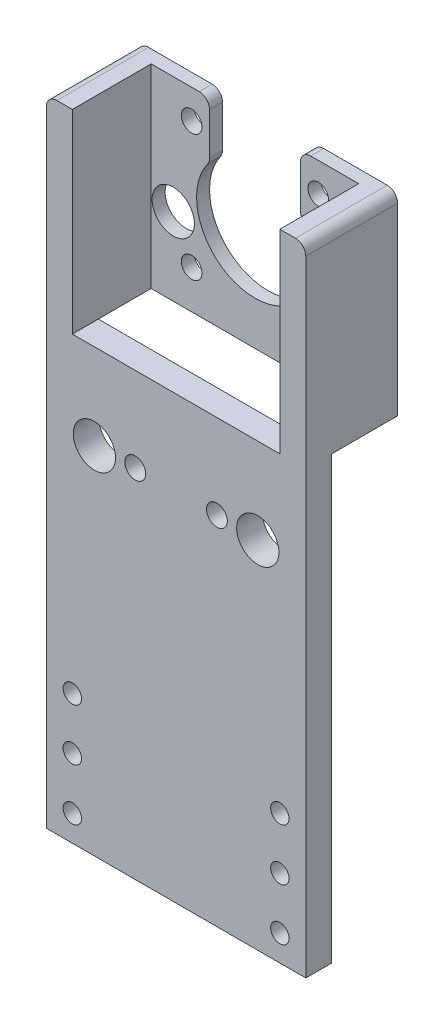
SolidWorks part; units mm, degrees
other "Markup1"
sketch "Sketch16" plane through (-31.75, 101.6, 0) normal (-0.1781, 0.3829, 0.9065) x (0.9824, 0.1222, 0.1414)
material "PLA White"
ref_plane "Front Plane" through (0, 0, 0) normal (0, 0, 1) x (1, 0, 0)
ref_plane "Top Plane" through (0, 0, 0) normal (0, 1, 0) x (1, 0, 0)
ref_plane "Right Plane" through (0, 0, 0) normal (1, 0, 0) x (0, 0, -1)
sketch "Sketch1" plane through (0, 0, 0) normal (1, 0, 0) x (0, 0, -1)
  line L2 (0, -53.975) -> (0, 53.975)
  line L4 (6.35, -53.975) -> (6.35, 53.975)
  line L15 (6.35, -53.975) -> (0, -53.975)
  line L24 (6.35, 53.975) -> (0, 53.975)
  point P14 (0, 0)
  dimension "D3" = 6.35
  dimension "D4" = 107.95
extrude "Boss-Extrude1" add sketch "Sketch1" along normal mid plane 63.5
sketch "Sketch2" plane through (0, 0, 0) normal (0, 0, 1) x (1, 0, 0)
  line L0 (-25.4, 95.25) -> (-25.4, 101.6) construction
  line L2 (-31.75, 53.975) -> (-31.75, 101.6)
  line L3 (-31.75, 101.6) -> (-25.4, 101.6)
  line L4 (-25.4, 53.975) -> (-25.4, 95.25)
  line L5 (-25.4, 101.6) -> (25.4, 101.6)
  line L7 (-25.4, 95.25) -> (25.4, 95.25)
  line L10 (31.75, 53.975) -> (31.75, 101.6)
  line L11 (31.75, 101.6) -> (25.4, 101.6)
  line L12 (25.4, 53.975) -> (25.4, 95.25)
  line L13 (31.75, 53.975) -> (-31.75, 53.975) construction
  line L18 (-31.75, 53.975) -> (-25.4, 53.975)
  line L19 (25.4, 53.975) -> (31.75, 53.975)
  dimension "D1" = 6.35
  dimension "D2" = 41.275
extrude "Boss-Extrude2" add sketch "Sketch2" against normal blind 19.304
sketch "Sketch3" plane through (0, 0, -19.304) normal (0, 0, -1) x (-1, 0, 0)
  line L1 (-31.75, 101.6) -> (31.75, 101.6)
  line L2 (-31.75, 101.6) -> (-31.75, 53.975)
  line L3 (-31.75, 53.975) -> (31.75, 53.975)
  line L4 (31.75, 101.6) -> (31.75, 53.975)
extrude "Boss-Extrude3" add sketch "Sketch3" along normal blind 3.175
sketch "Sketch5" plane through (0, 0, -22.479) normal (0, 0, -1) x (-1, 0, 0)
  line L0 (-11.1125, 87.9053) -> (-11.1125, 101.6)
  line L1 (31.75, 101.6) -> (-31.75, 101.6) construction
  line L2 (-11.1125, 101.6) -> (11.1125, 101.6)
  line L3 (11.1125, 101.6) -> (11.1125, 87.9053)
  arc A0 (11, 78.925) -> (-11, 78.925) centre (0, 78.925) ccw construction
  arc A1 (16.75, 63.425) -> (14.25, 63.425) centre (15.5, 63.425) ccw construction
  arc A2 (-14.25, 63.425) -> (-16.75, 63.425) centre (-15.5, 63.425) ccw construction
  arc A3 (-16.75, 94.425) -> (-14.25, 94.425) centre (-15.5, 94.425) ccw construction
  arc A4 (16.75, 94.425) -> (14.25, 94.425) centre (15.5, 94.425) ccw construction
  arc A5 (11, 78.925) -> (-11, 78.925) centre (0, 78.925) ccw construction
  arc A6 (16.75, 63.425) -> (14.25, 63.425) centre (15.5, 63.425) ccw construction
  arc A7 (-14.25, 63.425) -> (-16.75, 63.425) centre (-15.5, 63.425) ccw construction
  arc A8 (-16.75, 94.425) -> (-14.25, 94.425) centre (-15.5, 94.425) ccw construction
  arc A9 (16.75, 94.425) -> (14.25, 94.425) centre (15.5, 94.425) ccw construction
  arc A10 (-11.1125, 87.9053) -> (11.1125, 87.9053) centre (0, 78.925) ccw
  circle A11 centre (15.5, 94.425) radius 2.54
  circle A12 centre (15.5, 63.425) radius 2.54
  circle A13 centre (-15.5, 63.425) radius 2.54
  circle A14 centre (-15.5, 94.425) radius 2.54
  dimension "D1" = 5.08
  dimension "D2" = 28.575
  dimension "D3" = 22.225
extrude "Cut-Extrude2" cut sketch "Sketch5" against normal through all
fillet "Fillet1" radius 2.54 6 edges at (-31.75, 101.6, -11.2395) (31.75, 101.6, -11.2395) (-11.1125, 87.9053, -20.8915) (11.1125, 87.9053, -20.8915) (11.1125, 101.6, -11.2395) (-11.1125, 101.6, -11.2395)
sketch "Sketch7" plane through (0, 101.6, 0) normal (0, 1, 0) x (1, 0, 0)
  line L0 (29.21, 0) -> (13.6525, 0) construction
  line L1 (-25.4, 0) -> (25.4, 0)
  line L2 (-25.4, 0) -> (-25.4, 19.304)
  line L3 (-25.4, 19.304) -> (25.4, 19.304)
  line L4 (25.4, 0) -> (25.4, 19.304)
  line L5 (-14.2875, 19.304) -> (14.2875, 19.304) construction
  line L7 (-25.4, 19.304) -> (-25.4, 0) construction
  point P9 (0, 0)
extrude "Cut-Extrude4" cut sketch "Sketch7" against normal up to next
sketch "Sketch9" plane through (0, 0, 0) normal (0, 0, 1) x (1, 0, 0)
  line L0 (-25.4, -47.625) -> (25.4, -47.625) construction
  line L1 (31.75, 99.06) -> (31.75, -53.975) construction
  line L3 (31.75, -53.975) -> (-31.75, -53.975) construction
  circle A2 centre (25.4, -47.625) radius 2.25
  circle A3 centre (-25.4, -47.625) radius 2.25
  point P0 (0, -47.625)
  dimension "D3" = 4.5
  dimension "D1" = 6.35
  dimension "D2" = 6.35
extrude "Cut-Extrude5" cut sketch "Sketch9" against normal through all
sketch "Sketch15" plane through (0, 0, 0) normal (0, 0, 1) x (1, 0, 0)
  circle A0 centre (-20, 32.981) radius 2 construction
  circle A1 centre (20, 32.981) radius 2 construction
  circle A2 centre (20, 72.981) radius 2 construction
  circle A3 centre (-20, 72.981) radius 2 construction
  circle A4 centre (10, 72.981) radius 2.55 construction
  arc A5 (12.55, 33.281) -> (7.45, 33.281) centre (10, 33.281) ccw construction
  circle A6 centre (-10, 33.281) radius 2.55 construction
  arc A7 (-12.55, 72.981) -> (-7.45, 72.981) centre (-10, 72.981) ccw construction
  circle A8 centre (-20, 32.981) radius 2 construction
  circle A9 centre (20, 32.981) radius 2 construction
  circle A10 centre (20, 72.981) radius 2 construction
  circle A11 centre (-20, 72.981) radius 2 construction
  circle A12 centre (10, 72.981) radius 2.55
  arc A13 (12.55, 33.281) -> (7.45, 33.281) centre (10, 33.281) ccw
  circle A14 centre (-10, 33.281) radius 2.55
  arc A15 (-12.55, 72.981) -> (-7.45, 72.981) centre (-10, 72.981) ccw
  circle A16 centre (-10, 72.981) radius 2.55
  circle A17 centre (10, 33.281) radius 2.55
  circle A18 centre (-20, 72.981) radius 5.175
  circle A19 centre (20, 72.981) radius 5.175
  circle A20 centre (20, 32.981) radius 5.175
  circle A21 centre (-20, 32.981) radius 5.175
  dimension "D1" = 3.175
extrude "Cut-Extrude8" cut sketch "Sketch15" against normal through all contours A11 | A15 A16 | A12 | A10 | A13 A17 | A9 | A14 | A8 | A18 | A21 | A20 | A19
pattern_linear "LPattern1" count 3 spacing 12.7 along (0, 1, 0) of "Cut-Extrude5"
